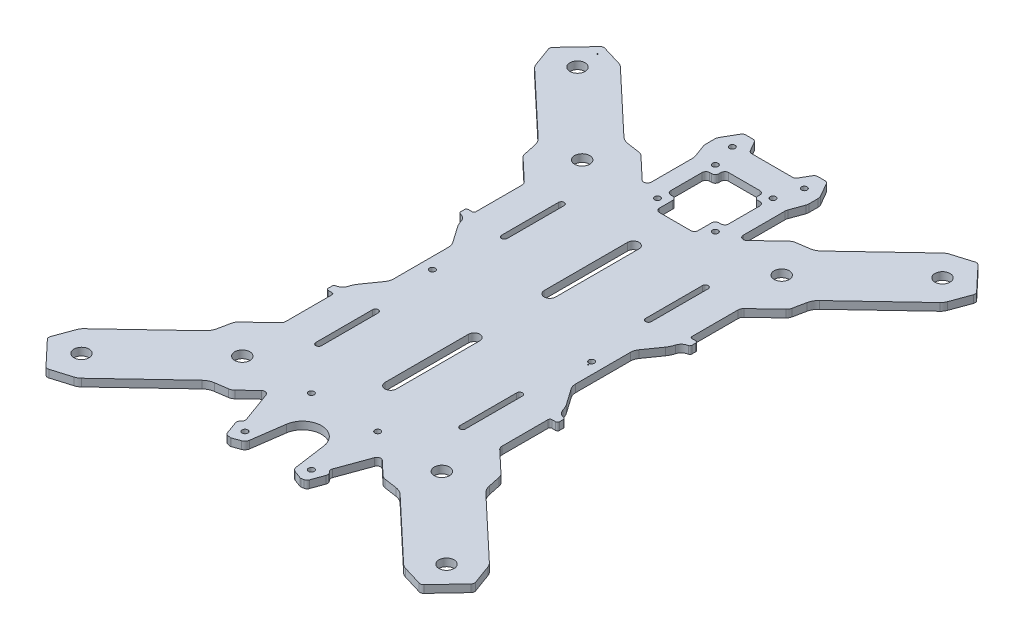
SolidWorks part; units mm, degrees
ref_plane "Front Plane" through (0, 0, 0) normal (0, 0, 1) x (1, 0, 0)
ref_plane "Top Plane" through (0, 0, 0) normal (0, 1, 0) x (1, 0, 0)
ref_plane "Right Plane" through (0, 0, 0) normal (1, 0, 0) x (0, 0, -1)
sketch "Sketch1" plane through (0, 0, 0) normal (0, 1, 0) x (1, 0, 0)
  line L0 (-19.6249, 134.6917) -> (-13.0182, 135.6588)
  line L1 (-8.6876, 137.755) -> (24.0914, 168.6751)
  line L2 (26.478, 170.0555) -> (36.7845, 173.16)
  line L3 (50.8434, 159.867) -> (38.8162, 172.6174)
  line L4 (51.2667, 157.8072) -> (47.5664, 147.6992)
  line L5 (46.0492, 145.3972) -> (13.2702, 114.4772)
  line L6 (10.925, 110.2761) -> (9.5742, 103.7371)
  line L7 (8.4017, 101.6366) -> (-2.966, 90.9136)
  line L8 (-3.9075, 64.4645) -> (-3.9074, 88.7313)
  line L9 (-0.9075, 63.4645) -> (-2.9075, 63.4645)
  line L10 (0.0925, 60.3756) -> (0.0925, 62.4645)
  line L11 (-6.0776, 52.5816) -> (-11.8224, 44.3773)
  line L12 (-12.9075, 12.0669) -> (-12.9075, 40.9358)
  line L13 (-11.8224, 8.6255) -> (-6.0776, 0.4211)
  line L14 (0.0925, -9.4618) -> (0.0925, -7.3729)
  line L15 (-2.9075, -10.4618) -> (-0.9075, -10.4618)
  line L16 (-3.9075, -35.7286) -> (-3.9075, -11.4618)
  line L17 (-2.966, -37.9109) -> (8.4016, -48.6339)
  line L18 (9.5742, -50.7344) -> (10.925, -57.2734)
  line L19 (13.2702, -61.4745) -> (46.0491, -92.3945)
  line L20 (47.5664, -94.6965) -> (51.2666, -104.8045)
  line L21 (38.8162, -119.6147) -> (50.8434, -106.8643)
  line L22 (36.7845, -120.1573) -> (26.478, -117.0528)
  line L23 (24.0914, -115.6724) -> (-8.6876, -84.7523)
  line L24 (-13.0182, -82.6561) -> (-19.6249, -81.689)
  line L25 (-21.7902, -80.6409) -> (-29.0255, -73.8159)
  line L26 (-38.2064, -90.8769) -> (-32.2772, -74.5867)
  line L27 (-37.8591, -92.8466) -> (-37.3024, -93.51)
  line L28 (-36.9551, -95.4796) -> (-39.3247, -101.99)
  line L29 (-40.8568, -103.2756) -> (-42.1762, -103.5082)
  line L30 (-42.6918, -103.4631) -> (-46.6699, -102.0152)
  line L31 (-48.6146, -99.6136) -> (-51.0048, -82.6069)
  line L32 (-70.8101, -82.6069) -> (-73.2003, -99.6136)
  line L33 (-75.145, -102.0152) -> (-79.123, -103.4631)
  line L34 (-80.9581, -103.2756) -> (-79.6387, -103.5082)
  line L35 (-84.8598, -95.4796) -> (-82.4902, -101.99)
  line L36 (-83.9558, -92.8466) -> (-84.5125, -93.51)
  line L37 (-89.5377, -74.5867) -> (-83.6085, -90.877)
  line L38 (-100.0247, -80.6409) -> (-92.7894, -73.8159)
  line L39 (-108.7967, -82.6561) -> (-102.19, -81.689)
  line L40 (-145.9063, -115.6724) -> (-113.1273, -84.7523)
  line L41 (-158.5994, -120.1573) -> (-148.2929, -117.0528)
  line L42 (-172.6583, -106.8643) -> (-160.6311, -119.6147)
  line L43 (-169.3813, -94.6965) -> (-173.0816, -104.8044)
  line L44 (-135.0851, -61.4744) -> (-167.864, -92.3945)
  line L45 (-131.3891, -50.7344) -> (-132.7399, -57.2734)
  line L46 (-118.8489, -37.9108) -> (-130.2166, -48.6338)
  line L47 (-117.9074, -11.4618) -> (-117.9074, -35.7285)
  line L48 (-120.9074, -10.4618) -> (-118.9074, -10.4618)
  line L49 (-121.9074, -7.3729) -> (-121.9074, -9.4618)
  line L50 (-109.9925, 8.6255) -> (-115.7373, 0.4211)
  line L51 (-108.9074, 40.9358) -> (-108.9074, 12.0669)
  line L52 (-115.7373, 52.5816) -> (-109.9925, 44.3773)
  line L53 (-121.9074, 62.4645) -> (-121.9074, 60.3756)
  line L54 (-118.9074, 63.4645) -> (-120.9074, 63.4645)
  line L55 (-117.9074, 88.7313) -> (-117.9074, 64.4645)
  line L56 (-130.2166, 101.6366) -> (-118.8489, 90.9136)
  line L57 (-132.7399, 110.2762) -> (-131.3891, 103.7371)
  line L58 (-167.864, 145.3973) -> (-135.0851, 114.4772)
  line L59 (-173.0816, 157.8072) -> (-169.3813, 147.6993)
  line L60 (-160.6311, 172.6174) -> (-172.6583, 159.8671)
  line L61 (-148.2929, 170.0555) -> (-158.5994, 173.1601)
  line L62 (-113.1273, 137.755) -> (-145.9063, 168.6751)
  line L63 (-102.19, 134.6917) -> (-108.7967, 135.6589)
  line L64 (-88.5298, 122.8006) -> (-100.0247, 133.6436)
  line L65 (-85.1574, 146.2232) -> (-85.1574, 124.2555)
  line L66 (-87.9162, 154.5082) -> (-85.3987, 147.5913)
  line L67 (-88.1574, 160.6375) -> (-88.1574, 155.8763)
  line L68 (-83.5386, 169.7093) -> (-87.6215, 162.6375)
  line L69 (-78.0083, 170.7093) -> (-81.8066, 170.7093)
  line L70 (-73.3895, 164.7093) -> (-76.2762, 169.7093)
  line L71 (-50.1574, 163.7092) -> (-71.6574, 163.7093)
  line L72 (-48.4254, 164.7092) -> (-45.5386, 169.7092)
  line L73 (-43.8066, 170.7092) -> (-40.0083, 170.7092)
  line L74 (-38.2762, 169.7092) -> (-34.1933, 162.6374)
  line L75 (-33.6574, 160.6374) -> (-33.6574, 155.8763)
  line L76 (-33.8987, 154.5082) -> (-36.4162, 147.5913)
  line L77 (-36.6574, 146.2232) -> (-36.6574, 124.2555)
  line L78 (-33.2851, 122.8006) -> (-21.7902, 133.6436)
  line L79 (-100.4074, -37.4986) -> (-100.4074, -7.4986)
  line L80 (-97.4074, -7.4986) -> (-97.4074, -37.4986)
  line L81 (-21.4074, 90.5014) -> (-21.4074, 60.5014)
  line L82 (-24.4074, 60.5014) -> (-24.4074, 90.5014)
  line L83 (-73.1574, 123.5014) -> (-74.1574, 123.5014)
  line L84 (-71.1574, 114.5014) -> (-71.1574, 121.5014)
  line L85 (-52.6574, 112.5014) -> (-69.1574, 112.5014)
  line L86 (-50.6574, 121.5014) -> (-50.6574, 114.5014)
  line L87 (-47.6574, 123.5014) -> (-48.6574, 123.5014)
  line L88 (-45.6574, 142.0014) -> (-45.6574, 125.5014)
  line L89 (-48.6574, 144.0014) -> (-47.6574, 144.0014)
  line L90 (-50.6574, 147.0014) -> (-50.6574, 146.0014)
  line L91 (-69.1574, 149.0014) -> (-52.6574, 149.0014)
  line L92 (-71.1574, 146.0014) -> (-71.1574, 147.0014)
  line L93 (-74.1574, 144.0014) -> (-73.1574, 144.0014)
  line L94 (-76.1574, 125.5014) -> (-76.1574, 142.0014)
  line L95 (-57.9074, 90.5014) -> (-57.9074, 46.5014)
  line L96 (-63.9074, 46.5014) -> (-63.9074, 90.5014)
  line L97 (-63.9074, -37.4986) -> (-63.9074, 6.5014)
  line L98 (-57.9074, 6.5014) -> (-57.9074, -37.4986)
  line L99 (-97.4074, 90.5014) -> (-97.4074, 60.5014)
  line L100 (-100.4074, 60.5014) -> (-100.4074, 90.5014)
  line L101 (-24.4074, -37.4986) -> (-24.4074, -7.4986)
  line L102 (-21.4074, -7.4986) -> (-21.4074, -37.4986)
  line L103 (-157.9145, 169.06) -> (-157.9134, 169.568)
  line L104 (-18.0443, 23.7445) -> (-17.7376, 23.3395)
  arc A0 (-19.6249, 134.6917) -> (-21.7902, 133.6436) centre (-19.0455, 130.7339) ccw
  arc A1 (-13.0182, 135.6588) -> (-8.6876, 137.755) centre (-14.177, 143.5745) ccw
  arc A2 (26.478, 170.0555) -> (24.0914, 168.6751) centre (28.2085, 164.3105) ccw
  arc A3 (38.8162, 172.6174) -> (36.7845, 173.16) centre (37.3613, 171.245) ccw
  arc A4 (51.2667, 157.8072) -> (50.8434, 159.867) centre (49.3886, 158.4947) ccw
  arc A5 (46.0492, 145.3972) -> (47.5664, 147.6992) centre (41.9321, 149.7618) ccw
  arc A6 (13.2702, 114.4772) -> (10.925, 110.2761) centre (18.7596, 108.6577) ccw
  arc A7 (8.4017, 101.6366) -> (9.5742, 103.7371) centre (5.657, 104.5463) ccw
  arc A8 (-2.966, 90.9136) -> (-3.9074, 88.7313) centre (-0.9074, 88.7313) ccw
  arc A9 (-3.9075, 64.4645) -> (-2.9075, 63.4645) centre (-2.9075, 64.4645) ccw
  arc A10 (0.0925, 62.4645) -> (-0.9075, 63.4645) centre (-0.9075, 62.4645) ccw
  arc A11 (-0.731, 59.3913) -> (0.0925, 60.3756) centre (-0.9075, 60.3756) ccw
  arc A12 (-0.731, 59.3913) -> (-4.3875, 56.1045) centre (0.0925, 54.7979) ccw
  arc A13 (-6.0776, 52.5816) -> (-4.3875, 56.1045) centre (-15.9075, 59.4645) ccw
  arc A14 (-11.8224, 44.3773) -> (-12.9075, 40.9358) centre (-6.9075, 40.9358) ccw
  arc A15 (-12.9075, 12.0669) -> (-11.8224, 8.6255) centre (-6.9075, 12.0669) ccw
  arc A16 (-4.3875, -3.1018) -> (-6.0776, 0.4211) centre (-15.9075, -6.4618) ccw
  arc A17 (-4.3875, -3.1018) -> (-0.731, -6.3886) centre (0.0925, -1.7951) ccw
  arc A18 (0.0925, -7.3729) -> (-0.731, -6.3886) centre (-0.9075, -7.3729) ccw
  arc A19 (-0.9075, -10.4618) -> (0.0925, -9.4618) centre (-0.9075, -9.4618) ccw
  arc A20 (-2.9075, -10.4618) -> (-3.9075, -11.4618) centre (-2.9075, -11.4618) ccw
  arc A21 (-3.9075, -35.7286) -> (-2.966, -37.9109) centre (-0.9075, -35.7286) ccw
  arc A22 (9.5742, -50.7344) -> (8.4016, -48.6339) centre (5.6569, -51.5436) ccw
  arc A23 (10.925, -57.2734) -> (13.2702, -61.4745) centre (18.7596, -55.655) ccw
  arc A24 (47.5664, -94.6965) -> (46.0491, -92.3945) centre (41.932, -96.7591) ccw
  arc A25 (50.8434, -106.8643) -> (51.2666, -104.8045) centre (49.3885, -105.492) ccw
  arc A26 (36.7845, -120.1573) -> (38.8162, -119.6147) centre (37.3613, -118.2423) ccw
  arc A27 (24.0914, -115.6724) -> (26.478, -117.0528) centre (28.2085, -111.3078) ccw
  arc A28 (-8.6876, -84.7523) -> (-13.0182, -82.6561) centre (-14.177, -90.5717) ccw
  arc A29 (-21.7902, -80.6409) -> (-19.6249, -81.689) centre (-19.0455, -77.7311) ccw
  arc A30 (-29.0255, -73.8159) -> (-32.2772, -74.5867) centre (-30.3978, -75.2708) ccw
  arc A31 (-38.2064, -90.8769) -> (-37.8591, -92.8466) centre (-36.327, -91.561) ccw
  arc A32 (-36.9551, -95.4796) -> (-37.3024, -93.51) centre (-38.8345, -94.7956) ccw
  arc A33 (-40.8568, -103.2756) -> (-39.3247, -101.99) centre (-41.2041, -101.3059) ccw
  arc A34 (-42.6918, -103.4631) -> (-42.1762, -103.5082) centre (-42.3498, -102.5234) ccw
  arc A35 (-48.6146, -99.6136) -> (-46.6699, -102.0152) centre (-45.6438, -99.1961) ccw
  arc A36 (-51.0048, -82.6069) -> (-70.8101, -82.6069) centre (-60.9074, -83.9986) ccw
  arc A37 (-75.145, -102.0152) -> (-73.2003, -99.6136) centre (-76.1711, -99.1961) ccw
  arc A38 (-79.6387, -103.5082) -> (-79.123, -103.4631) centre (-79.4651, -102.5234) ccw
  arc A39 (-82.4902, -101.99) -> (-80.9581, -103.2756) centre (-80.6108, -101.3059) ccw
  arc A40 (-84.5125, -93.51) -> (-84.8598, -95.4796) centre (-82.9804, -94.7956) ccw
  arc A41 (-83.9558, -92.8466) -> (-83.6085, -90.877) centre (-85.4879, -91.561) ccw
  arc A42 (-89.5377, -74.5867) -> (-92.7894, -73.8159) centre (-91.417, -75.2708) ccw
  arc A43 (-102.19, -81.689) -> (-100.0247, -80.6409) centre (-102.7694, -77.7311) ccw
  arc A44 (-108.7967, -82.6561) -> (-113.1273, -84.7523) centre (-107.6379, -90.5717) ccw
  arc A45 (-148.2929, -117.0528) -> (-145.9063, -115.6724) centre (-150.0234, -111.3078) ccw
  arc A46 (-160.6311, -119.6147) -> (-158.5994, -120.1573) centre (-159.1762, -118.2423) ccw
  arc A47 (-173.0816, -104.8044) -> (-172.6583, -106.8643) centre (-171.2035, -105.492) ccw
  arc A48 (-167.864, -92.3945) -> (-169.3813, -94.6965) centre (-163.747, -96.7591) ccw
  arc A49 (-135.0851, -61.4744) -> (-132.7399, -57.2734) centre (-140.5745, -55.655) ccw
  arc A50 (-130.2166, -48.6338) -> (-131.3891, -50.7344) centre (-127.4718, -51.5436) ccw
  arc A51 (-118.8489, -37.9108) -> (-117.9074, -35.7285) centre (-120.9074, -35.7285) ccw
  arc A52 (-117.9074, -11.4618) -> (-118.9074, -10.4618) centre (-118.9074, -11.4618) ccw
  arc A53 (-121.9074, -9.4618) -> (-120.9074, -10.4618) centre (-120.9074, -9.4618) ccw
  arc A54 (-121.0839, -6.3885) -> (-121.9074, -7.3729) centre (-120.9074, -7.3729) ccw
  arc A55 (-121.0839, -6.3885) -> (-117.4274, -3.1018) centre (-121.9074, -1.7951) ccw
  arc A56 (-115.7373, 0.4211) -> (-117.4274, -3.1018) centre (-105.9074, -6.4618) ccw
  arc A57 (-109.9925, 8.6255) -> (-108.9074, 12.0669) centre (-114.9074, 12.0669) ccw
  arc A58 (-108.9074, 40.9358) -> (-109.9925, 44.3773) centre (-114.9074, 40.9358) ccw
  arc A59 (-117.4274, 56.1045) -> (-115.7373, 52.5816) centre (-105.9074, 59.4645) ccw
  arc A60 (-117.4274, 56.1045) -> (-121.0839, 59.3913) centre (-121.9074, 54.7979) ccw
  arc A61 (-121.9074, 60.3756) -> (-121.0839, 59.3913) centre (-120.9074, 60.3756) ccw
  arc A62 (-120.9074, 63.4645) -> (-121.9074, 62.4645) centre (-120.9074, 62.4645) ccw
  arc A63 (-118.9074, 63.4645) -> (-117.9074, 64.4645) centre (-118.9074, 64.4645) ccw
  arc A64 (-117.9074, 88.7313) -> (-118.8489, 90.9136) centre (-120.9074, 88.7313) ccw
  arc A65 (-131.3891, 103.7371) -> (-130.2166, 101.6366) centre (-127.4718, 104.5463) ccw
  arc A66 (-132.7399, 110.2762) -> (-135.0851, 114.4772) centre (-140.5745, 108.6577) ccw
  arc A67 (-169.3813, 147.6993) -> (-167.864, 145.3973) centre (-163.747, 149.7619) ccw
  arc A68 (-172.6583, 159.8671) -> (-173.0816, 157.8072) centre (-171.2035, 158.4947) ccw
  arc A69 (-158.5994, 173.1601) -> (-160.6311, 172.6174) centre (-159.1762, 171.2451) ccw
  arc A70 (-145.9063, 168.6751) -> (-148.2929, 170.0555) centre (-150.0234, 164.3105) ccw
  arc A71 (-113.1273, 137.755) -> (-108.7967, 135.6589) centre (-107.6379, 143.5745) ccw
  arc A72 (-100.0247, 133.6436) -> (-102.19, 134.6917) centre (-102.7694, 130.7339) ccw
  arc A73 (-88.5298, 122.8006) -> (-85.1574, 124.2555) centre (-87.1574, 124.2555) ccw
  arc A74 (-85.1574, 146.2232) -> (-85.3987, 147.5913) centre (-89.1574, 146.2232) ccw
  arc A75 (-88.1574, 155.8763) -> (-87.9162, 154.5082) centre (-84.1574, 155.8763) ccw
  arc A76 (-87.6215, 162.6375) -> (-88.1574, 160.6375) centre (-84.1574, 160.6375) ccw
  arc A77 (-81.8066, 170.7093) -> (-83.5386, 169.7093) centre (-81.8066, 168.7093) ccw
  arc A78 (-76.2762, 169.7093) -> (-78.0083, 170.7093) centre (-78.0083, 168.7093) ccw
  arc A79 (-73.3895, 164.7093) -> (-71.6574, 163.7093) centre (-71.6574, 165.7093) ccw
  arc A80 (-50.1574, 163.7092) -> (-48.4254, 164.7092) centre (-50.1574, 165.7092) ccw
  arc A81 (-43.8066, 170.7092) -> (-45.5386, 169.7092) centre (-43.8066, 168.7092) ccw
  arc A82 (-38.2762, 169.7092) -> (-40.0083, 170.7092) centre (-40.0083, 168.7092) ccw
  arc A83 (-33.6574, 160.6374) -> (-34.1933, 162.6374) centre (-37.6574, 160.6374) ccw
  arc A84 (-33.8987, 154.5082) -> (-33.6574, 155.8763) centre (-37.6574, 155.8763) ccw
  arc A85 (-36.4162, 147.5913) -> (-36.6574, 146.2232) centre (-32.6574, 146.2232) ccw
  arc A86 (-36.6574, 124.2555) -> (-33.2851, 122.8006) centre (-34.6574, 124.2555) ccw
  arc A87 (-97.4074, -7.4986) -> (-100.4074, -7.4986) centre (-98.9074, -7.4986) ccw
  arc A88 (-100.4074, -37.4986) -> (-97.4074, -37.4986) centre (-98.9074, -37.4986) ccw
  arc A89 (-24.4074, 60.5014) -> (-21.4074, 60.5014) centre (-22.9074, 60.5014) ccw
  arc A90 (-21.4074, 90.5014) -> (-24.4074, 90.5014) centre (-22.9074, 90.5014) ccw
  arc A91 (-76.1574, 125.5014) -> (-74.1574, 123.5014) centre (-74.1574, 125.5014) ccw
  arc A92 (-71.1574, 121.5014) -> (-73.1574, 123.5014) centre (-73.1574, 121.5014) ccw
  arc A93 (-71.1574, 114.5014) -> (-69.1574, 112.5014) centre (-69.1574, 114.5014) ccw
  arc A94 (-52.6574, 112.5014) -> (-50.6574, 114.5014) centre (-52.6574, 114.5014) ccw
  arc A95 (-48.6574, 123.5014) -> (-50.6574, 121.5014) centre (-48.6574, 121.5014) ccw
  arc A96 (-47.6574, 123.5014) -> (-45.6574, 125.5014) centre (-47.6574, 125.5014) ccw
  arc A97 (-45.6574, 142.0014) -> (-47.6574, 144.0014) centre (-47.6574, 142.0014) ccw
  arc A98 (-50.6574, 146.0014) -> (-48.6574, 144.0014) centre (-48.6574, 146.0014) ccw
  arc A99 (-50.6574, 147.0014) -> (-52.6574, 149.0014) centre (-52.6574, 147.0014) ccw
  arc A100 (-69.1574, 149.0014) -> (-71.1574, 147.0014) centre (-69.1574, 147.0014) ccw
  arc A101 (-73.1574, 144.0014) -> (-71.1574, 146.0014) centre (-73.1574, 146.0014) ccw
  arc A102 (-74.1574, 144.0014) -> (-76.1574, 142.0014) centre (-74.1574, 142.0014) ccw
  circle A103 centre (-45.6574, 118.5014) radius 1.5
  circle A104 centre (-76.1574, 149.0014) radius 1.5
  circle A105 centre (-43.4074, -61.8537) radius 1.5
  arc A106 (-63.9074, 46.5014) -> (-57.9074, 46.5014) centre (-60.9074, 46.5014) ccw
  arc A107 (-57.9074, 90.5014) -> (-63.9074, 90.5014) centre (-60.9074, 90.5014) ccw
  circle A108 centre (-78.4074, -96.8537) radius 1.5
  circle A109 centre (-113.5421, 116.1512) radius 4
  circle A110 centre (-157.1881, 157.3219) radius 4
  circle A111 centre (-113.5421, -63.1484) radius 4
  circle A112 centre (-157.1881, -104.3192) radius 4
  circle A113 centre (35.3732, -104.3192) radius 4
  circle A114 centre (-8.2727, -63.1484) radius 4
  circle A115 centre (35.3732, 157.3219) radius 4
  circle A116 centre (-8.2727, 116.1512) radius 4
  circle A117 centre (-43.4074, -96.8537) radius 1.5
  arc A118 (-57.9074, 6.5014) -> (-63.9074, 6.5014) centre (-60.9074, 6.5014) ccw
  arc A119 (-63.9074, -37.4986) -> (-57.9074, -37.4986) centre (-60.9074, -37.4986) ccw
  circle A120 centre (-78.4074, -61.8537) radius 1.5
  circle A121 centre (-45.6574, 149.0014) radius 1.5
  circle A122 centre (-76.1574, 118.5014) radius 1.5
  circle A123 centre (-79.9074, 161.7093) radius 3.5 construction
  circle A124 centre (-41.9074, 161.7093) radius 3.5 construction
  circle A125 centre (-102.9074, 26.5014) radius 3.5 construction
  circle A126 centre (-18.9074, 26.5014) radius 3.5 construction
  arc A127 (-100.4074, 60.5014) -> (-97.4074, 60.5014) centre (-98.9074, 60.5014) ccw
  arc A128 (-97.4074, 90.5014) -> (-100.4074, 90.5014) centre (-98.9074, 90.5014) ccw
  arc A129 (-21.4074, -7.4986) -> (-24.4074, -7.4986) centre (-22.9074, -7.4986) ccw
  arc A130 (-24.4074, -37.4986) -> (-21.4074, -37.4986) centre (-22.9074, -37.4986) ccw
  circle A131 centre (-18.9074, 26.5014) radius 1.5
  circle A132 centre (-102.9074, 26.5014) radius 1.5
  circle A133 centre (-41.9074, 161.7093) radius 1.5
  circle A134 centre (-79.9074, 161.7093) radius 1.5
  circle A135 centre (-157.9157, 168.552) radius 0.254
  circle A136 centre (-18.3509, 24.1496) radius 0.254
  point P377 (-97.4074, 75.5014)
  line B0 (61.7987, -0.091) -> (0, -0.091)
sketch_block_instance "SW_NOTE_4-1"
sketch_block "SW_NOTE_4"
other "DetailItem22"
other "DetailItem23"
other "DetailItem24" parameters "D2"=7, "D6"=8, "D9"=3, "D1"=30.5, "D3"=30.9201, "D4"=45.0612, "D5"=38, "D7"=35, "D8"=35, "D10"=84, "D11"=30, "D12"=44, "D13"=44, "D14"=30
extrude "Bottom Plate" add sketch "Sketch1" along normal blind 4 contours A86 L77 A85 L76 A84 L75 A83 L74 A82 L73 A81 L72 A80 L71 A79 L70 A78 L69 A77 L68 A76 L67 A75 L66 A74 L65 A73 L64 A72 L63 A71 L62 A70 L61 A69 L60 A68 L59 A67 L58 A66 L57 A65 L56 A64 L55 A63 L54 A62 L53 A61
